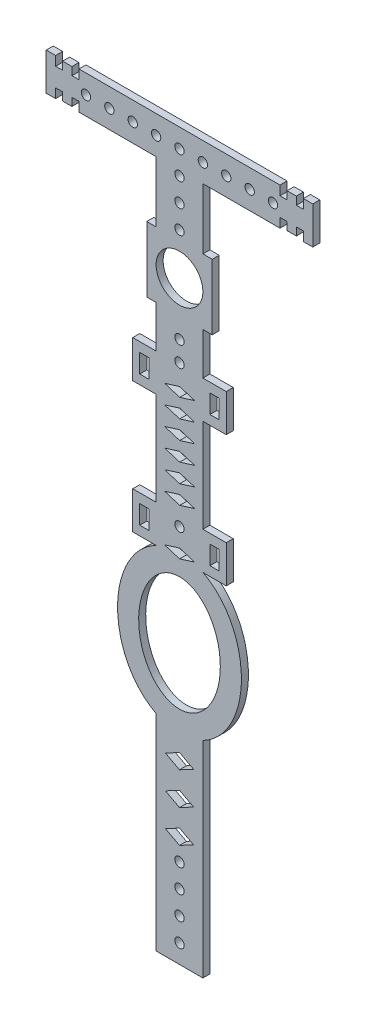
SolidWorks part; units mm, degrees
ref_plane "前视基准面" through (0, 0, 0) normal (0, 0, 1) x (1, 0, 0)
ref_plane "上视基准面" through (0, 0, 0) normal (0, 1, 0) x (1, 0, 0)
ref_plane "右视基准面" through (0, 0, 0) normal (1, 0, 0) x (0, 0, -1)
other "Configuration Table"
sketch "草图1" plane through (0, 0, 0) normal (0, 0, 1) x (1, 0, 0)
  line L0 (-21.4993, 30) -> (-21.4993, 28)
  line L1 (-21.4993, 28) -> (-22.9993, 28)
  line L2 (-22.9993, 29.7) -> (-24.9993, 29.7)
  line L3 (-7, 9) -> (-5, 9)
  line L4 (-7, 9) -> (-7, -5)
  line L5 (-7, -5) -> (-5, -5)
  line L6 (7, 9) -> (7, -5)
  line L7 (-7, 9) -> (7, -5) construction
  line L8 (-7, -5) -> (7, 9) construction
  line L9 (-24.9993, 29.7) -> (-24.9993, 28)
  line L10 (-26.4993, 28) -> (-26.4993, 30.4519)
  line L12 (-26.4993, 30) -> (-28.4993, 30)
  line L13 (-28.4993, 30) -> (-28.4993, 22)
  line L18 (-22.9993, 24) -> (-22.9993, 22.3)
  line L19 (-26.4993, 24) -> (-24.9993, 24)
  line L20 (0.0395, -36.0528) -> (3.2395, -35.0528)
  line L21 (-5, 9) -> (-5, 22)
  line L22 (-5, 22) -> (-21.4993, 22)
  line L23 (-26.4993, 22) -> (-28.4993, 22)
  line L24 (-26.4993, 24) -> (-26.4993, 22)
  line L26 (-24.9993, 22.3) -> (-24.9993, 24)
  line L27 (-22.9993, 22.3) -> (-24.9993, 22.3)
  line L29 (-21.4993, 24) -> (-22.9993, 24)
  line L30 (-21.4993, 22) -> (-21.4993, 24)
  line L35 (22.9993, 28) -> (22.9993, 29.7)
  line L36 (26.4993, 28) -> (24.9993, 28)
  line L42 (-26.4993, 28) -> (-24.9993, 28)
  line L43 (-22.9993, 28) -> (-22.9993, 29.7)
  line L46 (21.4993, 22) -> (21.4993, 24)
  line L47 (21.4993, 24) -> (22.9993, 24)
  line L48 (-21.4993, 30) -> (21.4993, 30)
  line L49 (-5, -5) -> (-5, -14)
  line L50 (-5, -14) -> (-10, -14)
  line L51 (-10, -14) -> (-10, -22)
  line L52 (-10, -22) -> (-5, -22)
  line L53 (-5, -22) -> (-5, -42)
  line L54 (-5, -42) -> (-10, -42)
  line L55 (-10, -42) -> (-10, -50)
  line L56 (-10, -50) -> (-5, -50)
  line L57 (-8.5, -16) -> (-6.5, -16)
  line L58 (-8.5, -16) -> (-8.5, -20)
  line L59 (-8.5, -20) -> (-6.5, -20)
  line L60 (-6.5, -16) -> (-6.5, -20)
  line L61 (-8.5, -16) -> (-6.5, -20) construction
  line L62 (-8.5, -20) -> (-6.5, -16) construction
  line L63 (-8.5, -44) -> (-6.5, -44)
  line L64 (-8.5, -44) -> (-8.5, -48)
  line L65 (-8.5, -48) -> (-6.5, -48)
  line L66 (-6.5, -44) -> (-6.5, -48)
  line L67 (-8.5, -44) -> (-6.5, -48) construction
  line L68 (-8.5, -48) -> (-6.5, -44) construction
  line L69 (5, 9) -> (5, 22)
  line L70 (22.9993, 22.3) -> (24.9993, 22.3)
  line L71 (24.9993, 22.3) -> (24.9993, 24)
  line L72 (26.4993, 24) -> (26.4993, 22)
  line L74 (26.4993, 22) -> (28.4993, 22)
  line L75 (26.4993, 24) -> (24.9993, 24)
  line L76 (22.9993, 24) -> (22.9993, 22.3)
  line L77 (28.4993, 30) -> (28.4993, 22)
  line L78 (26.4993, 30) -> (28.4993, 30)
  line L79 (5, 22) -> (21.4993, 22)
  line L80 (5, -5) -> (5, -14)
  line L81 (8.5, -48) -> (6.5, -44) construction
  line L82 (8.5, -44) -> (6.5, -48) construction
  line L83 (8.5, -20) -> (6.5, -16) construction
  line L84 (8.5, -16) -> (6.5, -20) construction
  line L85 (6.5, -44) -> (6.5, -48)
  line L86 (8.5, -48) -> (6.5, -48)
  line L87 (8.5, -44) -> (8.5, -48)
  line L88 (8.5, -44) -> (6.5, -44)
  line L89 (6.5, -16) -> (6.5, -20)
  line L90 (8.5, -20) -> (6.5, -20)
  line L91 (8.5, -16) -> (8.5, -20)
  line L92 (8.5, -16) -> (6.5, -16)
  line L93 (10, -50) -> (5, -50)
  line L94 (10, -42) -> (10, -50)
  line L95 (5, -42) -> (10, -42)
  line L96 (5, -22) -> (5, -42)
  line L97 (10, -22) -> (5, -22)
  line L98 (10, -14) -> (10, -22)
  line L99 (5, -14) -> (10, -14)
  line L100 (-5, -81.1196) -> (-5, -125.1196)
  line L102 (5, -125.1196) -> (5, -81.1196)
  line L107 (3, -101.4579) -> (0, -103.0613)
  line L108 (0, -103.0613) -> (-3, -101.4579)
  line L109 (-3, -101.4579) -> (0, -99.8545)
  line L110 (0, -99.8545) -> (3, -101.4579)
  line L111 (3, -94.4579) -> (0, -96.0613)
  line L112 (0, -96.0613) -> (-3, -94.4579)
  line L113 (-3, -94.4579) -> (0, -92.8545)
  line L114 (0, -92.8545) -> (3, -94.4579)
  line L115 (3, -87.4579) -> (0, -89.0613)
  line L116 (0, -89.0613) -> (-3, -87.4579)
  line L117 (-3, -87.4579) -> (0, -85.8545)
  line L118 (0, -85.8545) -> (3, -87.4579)
  line L119 (-5, -125.1196) -> (5, -125.1196)
  line L120 (-27.5, 26) -> (-15.7949, 26) construction
  line L121 (26.4993, 28) -> (26.4993, 30)
  line L123 (24.9993, 29.7) -> (24.9993, 28)
  line L124 (22.9993, 29.7) -> (24.9993, 29.7)
  line L125 (21.4993, 28) -> (22.9993, 28)
  line L126 (21.4993, 30) -> (21.4993, 28)
  line L127 (5, -5) -> (7, -5)
  line L128 (5, 9) -> (7, 9)
  line L144 (0.0395, -38.0528) -> (-3.1605, -39.0528)
  line L145 (-3.1605, -39.0528) -> (0.0395, -40.0528)
  line L146 (0.0395, -40.0528) -> (3.2395, -39.0528)
  line L147 (3.2395, -39.0528) -> (0.0395, -38.0528)
  line L148 (3.2395, -35.0528) -> (0.0395, -34.0528)
  line L149 (0.0395, -34.0528) -> (-3.1605, -35.0528)
  line L150 (-3.1605, -35.0528) -> (0.0395, -36.0528)
  line L151 (0.0395, -32.0528) -> (3.2395, -31.0528)
  line L152 (3.2395, -31.0528) -> (0.0395, -30.0528)
  line L153 (0.0395, -30.0528) -> (-3.1605, -31.0528)
  line L154 (-3.1605, -31.0528) -> (0.0395, -32.0528)
  line L155 (0.0395, -28.0528) -> (3.2395, -27.0528)
  line L156 (3.2395, -27.0528) -> (0.0395, -26.0528)
  line L157 (0.0395, -26.0528) -> (-3.1605, -27.0528)
  line L158 (-3.1605, -27.0528) -> (0.0395, -28.0528)
  line L159 (0.0395, -24.0528) -> (3.2395, -23.0528)
  line L160 (3.2395, -23.0528) -> (0.0395, -22.0528)
  line L161 (0.0395, -22.0528) -> (-3.1605, -23.0528)
  line L162 (-3.1605, -23.0528) -> (0.0395, -24.0528)
  line L163 (0.0395, -20.0528) -> (3.2395, -19.0528)
  line L164 (3.2395, -19.0528) -> (0.0395, -18.0528)
  line L165 (0.0395, -18.0528) -> (-3.1605, -19.0528)
  line L166 (-3.1605, -19.0528) -> (0.0395, -20.0528)
  line L171 (0.0395, -14.0528) -> (-3.1605, -15.0528) [skipped]
  line L172 (-3.1605, -15.0528) -> (0.0395, -16.0528) [skipped]
  line L173 (0.0395, -16.0528) -> (3.2395, -15.0528) [skipped]
  line L174 (3.2395, -15.0528) -> (0.0395, -14.0528) [skipped]
  line L175 (0, -39) -> (0, -44) construction
  line L180 (0.0201, -47.9781) -> (-3.1799, -48.9781)
  line L181 (-3.1799, -48.9781) -> (0.0201, -49.9781)
  line L182 (0.0201, -49.9781) -> (3.2201, -48.9781)
  line L183 (3.2201, -48.9781) -> (0.0201, -47.9781)
  circle A0 centre (0, 2) radius 5
  circle A2 centre (0, -121.1196) radius 1
  circle A3 centre (0, -116.1196) radius 1
  circle A4 centre (0, -44) radius 1
  circle A11 centre (0, -13.6667) radius 1
  circle A12 centre (0, -9.3333) radius 1
  circle A13 centre (0, 25.9514) radius 1
  circle A14 centre (5, 25.9514) radius 1
  circle A15 centre (10, 25.9514) radius 1
  circle A16 centre (15, 25.9514) radius 1
  circle A17 centre (20, 25.9514) radius 1
  circle A18 centre (-5, 25.9514) radius 1
  circle A19 centre (-10, 25.9514) radius 1
  circle A20 centre (-15, 25.9514) radius 1
  circle A21 centre (-20, 25.9514) radius 1
  circle A22 centre (0, 20.9514) radius 1
  circle A23 centre (0, 15.9514) radius 1
  circle A24 centre (0, 10.9514) radius 1
  circle A25 centre (0, -111.1196) radius 1
  circle A26 centre (0, -106.1196) radius 1
  circle A27 centre (0, -39.6667) radius 1 [skipped]
  circle A28 centre (0, -35.3333) radius 1 [skipped]
  circle A29 centre (0, -31) radius 1 [skipped]
  circle A30 centre (0, -26.6667) radius 1 [skipped]
  circle A31 centre (0, -22.3333) radius 1 [skipped]
  circle A32 centre (0, -18) radius 1 [skipped]
  ellipse E0 centre (0, -65.5598) end of major axis (0, -77.8215) minor radius 8.7277
  spline S1 degree 3 poles (-2.9572, -82.0581) (0, -82.472) (2.9572, -82.0581) (6.5802, -80.4965) (10.1362, -77.0656) (12.461, -72.0885) (13.2579, -67.5921) (13.2579, -63.5275) (12.461, -59.0311) (10.1362, -54.0539) (6.5802, -50.6231) (2.9572, -49.0614) (0, -48.6476) (-2.9572, -49.0614) (-6.5802, -50.6231) (-10.1362, -54.0539) (-12.461, -59.0311) (-13.2579, -63.5275) (-13.2579, -67.5921) (-12.461, -72.0885) (-10.1362, -77.0656) (-6.5802, -80.4965) (-2.9572, -82.0581) (0, -82.472) (2.9572, -82.0581) knots -0.785398 -0.392699 -0.19635 0 0.19635 0.392699 0.785398 1.178097 1.472622 1.668971 1.963495 2.356194 2.748894 2.945243 3.141593 3.337942 3.534292 3.926991 4.31969 4.614214 4.810564 5.105088 5.497787 5.890486 6.086836 6.283185 6.479535 6.675884 7.068583 only from (0, -82.334) to (0, -82.334)
  point P0 (-21.4993, 30)
  point P25 (-28.4993, 26)
  point P26 (0, -39)
  point P34 (-21.4993, 22)
  point P42 (-7.5, -46)
  point P45 (-7.5, -18)
  point P66 (-7.5, -18)
  point P72 (-13.2402, -65.5598)
  point P74 (13.2402, -65.5598)
  point P75 (-5, -50)
  point P77 (0.0395, -39.0528)
  point P81 (0, 30)
  point P107 (5, -50)
  point P108 (7.5, -18)
  point P109 (7.5, -46)
  point P150 (0, -49)
  point P182 (21.4993, 22)
  point P183 (28.4993, 26)
  point P184 (21.4993, 30)
  point P195 (-0.0194, -48.9253)
  point P196 (0.0201, -48.9781)
  dimension "D1" = 10
  dimension "D38" = 2
  dimension "D40" = 2
  dimension "D2" = 14
  dimension "D3" = 14
  dimension "D5" = 2
  dimension "D6" = 1.7
  dimension "D7" = 1.5
  dimension "D8" = 2
  dimension "D9" = 4
  dimension "D10" = 2
  dimension "D11" = 8
  dimension "D12" = 3
  dimension "D13" = 2
  dimension "D14" = 4
  dimension "D15" = 7
  dimension "D16" = 5
  dimension "D17" = 5
  dimension "D21" = 5
  dimension "D22" = 8
  dimension "D23" = 1.5
  dimension "D24" = 2
  dimension "D25" = 4
  dimension "D26" = 20
  dimension "D27" = 4
  dimension "D28" = 10
  dimension "D39" = 9
  dimension "D41" = 5
  dimension "D42" = 5
extrude "凸台-拉伸1" add sketch "草图1" along normal blind 1.5 contours S1 L93 L94 L95 L96 L97 L98 L99 L80 L127 L6 L128 L69 L79 L46 L47 L76 L70 L71 L75 L72 L74 L77 L78 L121 L36 L123 L124 L35 L125 L126 L48 L0 L1 L43 L2 L9 L42 L10 L12 L13 L23 L24 L19 L26 L27 L18 L29 L30 L22 L21 | S1 E0 | S1 L100 L119 L102 A26 A25 A3 A2 L109 L110 L107 L108 L113 L114 L111 L112 L117 L118 L115 L116
